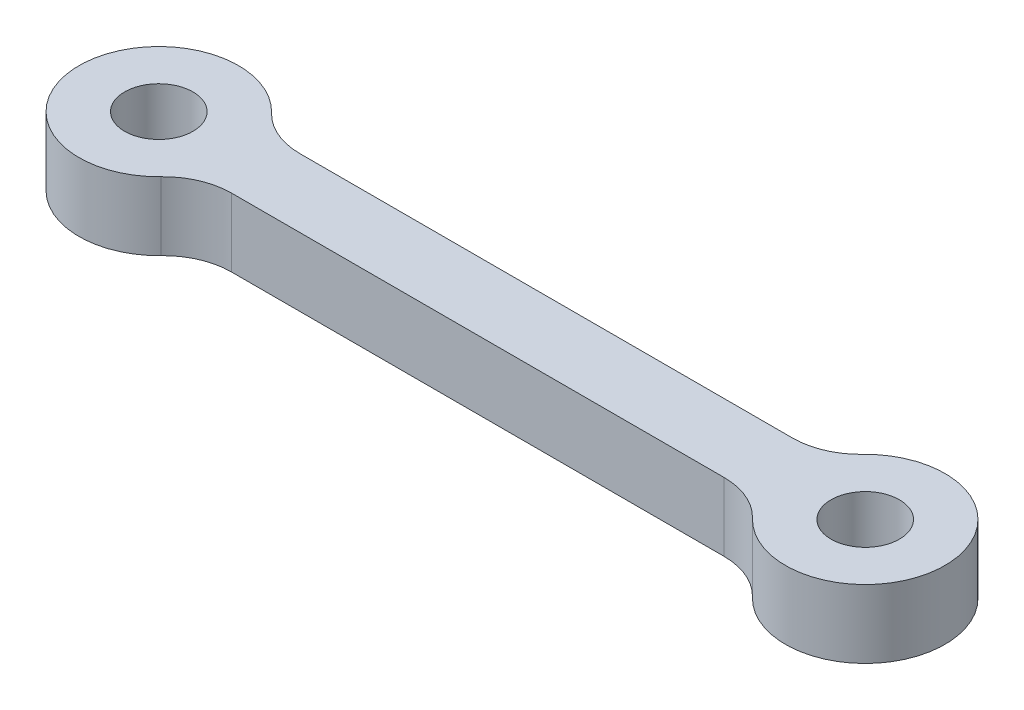
SolidWorks part; units mm, degrees
material "Wrought Stainless Steel"
ref_plane "Front Plane" through (0, 0, 0) normal (0, 0, 1) x (1, 0, 0)
ref_plane "Top Plane" through (0, 0, 0) normal (0, 1, 0) x (1, 0, 0)
ref_plane "Right Plane" through (0, 0, 0) normal (1, 0, 0) x (0, 0, -1)
sketch "Sketch1" plane through (0, 0, 0) normal (0, 1, 0) x (1, 0, 0)
  line L0 (-12.3377, 1.5) -> (12.3377, 1.5)
  line L3 (-12.3377, -1.5) -> (12.3377, -1.5)
  line L5 (-15.5, 1.5) -> (15.5, -1.5) construction
  line L6 (-15.5, -1.5) -> (15.5, 1.5) construction
  line L7 (0, 2.8044) -> (0, -3.1469) construction
  circle A0 centre (-15.5, 0) radius 1.5
  circle A1 centre (15.5, 0) radius 1.5
  arc A2 (-12.3377, 1.5) -> (-12.3377, -1.5) centre (-15.5, 0) ccw
  arc A3 (12.3377, 1.5) -> (12.3377, -1.5) centre (15.5, 0) cw
  point P0 (0, 0)
  dimension "D3" = 7
  dimension "D1" = 31
  dimension "D2" = 3
extrude "Boss-Extrude1" add sketch "Sketch1" along normal blind 3
fillet "Fillet1" radius 3 4 edges at (12.3377, 1.5, -1.5) (-12.3377, 1.5, -1.5) (12.3377, 1.5, 1.5) (-12.3377, 1.5, 1.5)
